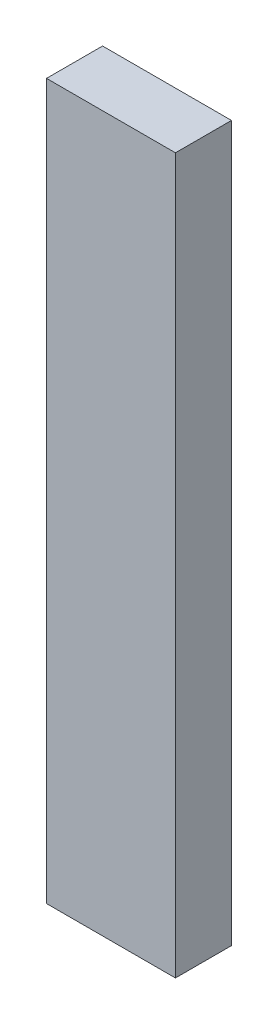
SolidWorks part; units mm, degrees
material "Pine"
ref_plane "Front Plane" through (0, 0, 0) normal (0, 0, 1) x (1, 0, 0)
ref_plane "Top Plane" through (0, 0, 0) normal (0, 1, 0) x (1, 0, 0)
ref_plane "Right Plane" through (0, 0, 0) normal (1, 0, 0) x (0, 0, -1)
sketch "Sketch1" plane through (0, 0, 0) normal (0, 1, 0) x (1, 0, 0)
  line L1 (-23, -10) -> (23, -10)
  line L2 (-23, -10) -> (-23, 10)
  line L3 (-23, 10) -> (23, 10)
  line L4 (23, -10) -> (23, 10)
  line L5 (-23, -10) -> (23, 10) construction
  line L6 (-23, 10) -> (23, -10) construction
  point P0 (0, 0)
  dimension "D1" = 46
  dimension "D2" = 20
extrude "Boss-Extrude1" add sketch "Sketch1" along normal blind 255
